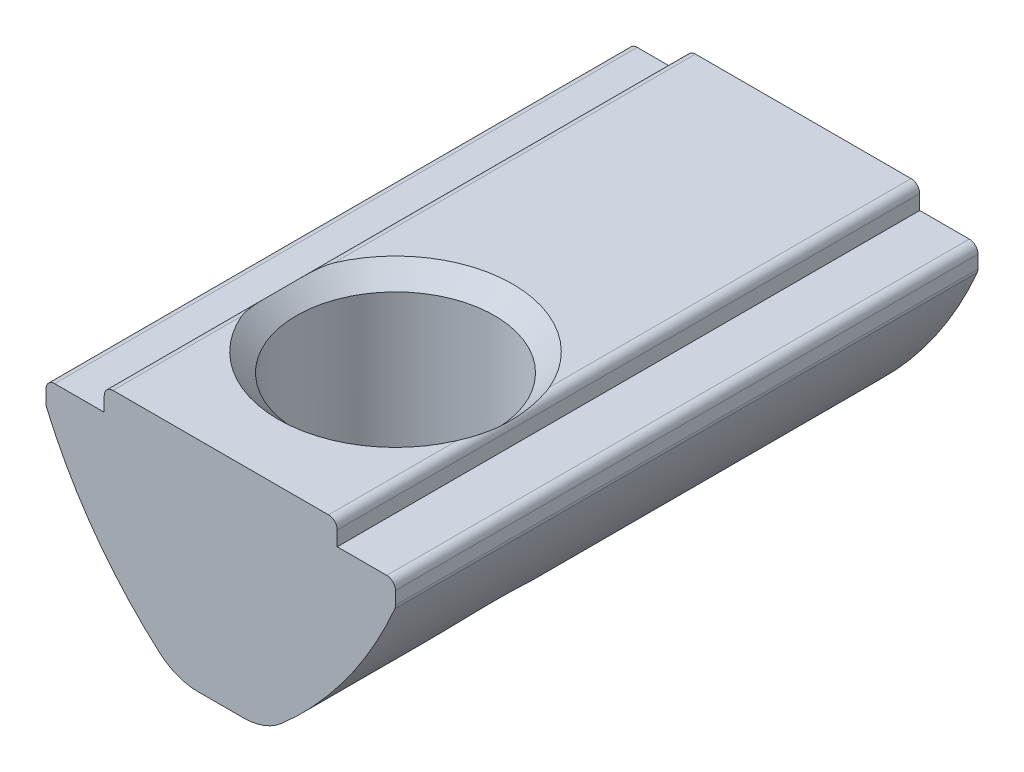
SolidWorks part; units mm, degrees
ref_plane "Спереди" through (0, 0, 0) normal (0, 0, 1) x (1, 0, 0)
ref_plane "Сверху" through (0, 0, 0) normal (0, 1, 0) x (1, 0, 0)
ref_plane "Справа" through (0, 0, 0) normal (1, 0, 0) x (0, 0, -1)
sketch "Эскиз1" plane through (0, 0, 0) normal (0, 0, 1) x (1, 0, 0)
  line L0 (-4, 0) -> (4, 0)
  line L5 (-4, 0) -> (-4, -0.8)
  line L6 (-4, -0.8) -> (-6, -0.8)
  line L7 (-6, -0.8) -> (-6, -1.6)
  line L8 (4, 0) -> (4, -0.8)
  line L9 (4, -0.8) -> (6, -0.8)
  line L10 (6, -0.8) -> (6, -1.6)
  line L11 (-1.5, -7.5) -> (1.5, -7.5)
  arc A0 (-6, -1.6) -> (-1.5, -7.5) centre (7.8062, 4.2641) ccw
  arc A1 (1.5, -7.5) -> (6, -1.6) centre (-7.8062, 4.2641) ccw
  point P0 (0, -7.5)
  point P4 (0, 0)
  dimension "D7" = 15
  dimension "D1" = 8
  dimension "D2" = 12
  dimension "D3" = 0.8
  dimension "D4" = 3
  dimension "D5" = 0.8
  dimension "D6" = 7.5
extrude "Бобышка-Вытянуть1" add sketch "Эскиз1" along normal mid plane 20
fillet "Скругление1" radius 0.3 6 edges at (6, -1.6, 0) (6, -0.8, 0) (-6, -0.8, 0) (-6, -1.6, 0) (4, 0, 0) (-4, 0, 0)
fillet "Скругление2" radius 2 2 edges at (1.5, -7.5, 0) (-1.5, -7.5, 0)
hole_wizard "Отверстие обработанное метчиком M81" positions "Эскиз2" profile "Эскиз4" tap size "M8" standard "ISO" end condition through all
sketch "Эскиз2" plane through (0, 0, 0) normal (0, 1, 0) x (1, 0, 0)
  line L0 (3.7, -10) -> (-3.7, -10) construction
  point P0 (0, -4)
  dimension "D1" = 6
sketch "Эскиз4" plane through (0, 0, 4) normal (1, 0, 0) x (0, 0, 1)
  line L0 (0, 0) -> (0, 7.5)
  line L1 (0, 7.5) -> (3.4, 7.5)
  line L2 (3.4, 7.5) -> (3.4, 0.625)
  line L3 (3.4, 0.625) -> (4.025, 0)
  line L5 (4.025, 0) -> (0, 0)
  line L6 (-3.4, 0.625) -> (-4.025, 0) construction
  line L11 (0, -6.35) -> (0, 107.95) construction
  dimension "Диаметр проходного сверла" = 6.8
  dimension "Глубина проходного сверла" = 7.5
  dimension "Диаметр передней зенковки" = 8.05
  dimension "Угол передней зенковки" = 90
cosmetic thread "Отверстие резьбы1" parameters "D2"=8
sketch "Эскиз5" plane through (0, 0, 0) normal (1, 0, 0) x (0, 0, -1)
  line L1 (6, -4.3) -> (6, -8.3) construction
  line L2 (10, -7.0022) -> (10, -1.657) construction
  line L3 (6, -4.3) -> (6, -8.3)
  line L5 (10, -7.5) -> (-0.6898, -7.5) construction
  arc A0 (6, -4.3) -> (6, -8.3) centre (6, -6.3) ccw
  point P3 (4, -7.4722)
  dimension "D3" = 2
  dimension "D1" = 0.8
  dimension "D2" = 4
revolve "Повернуть1" add sketch "Эскиз5" angle 360 about L1
